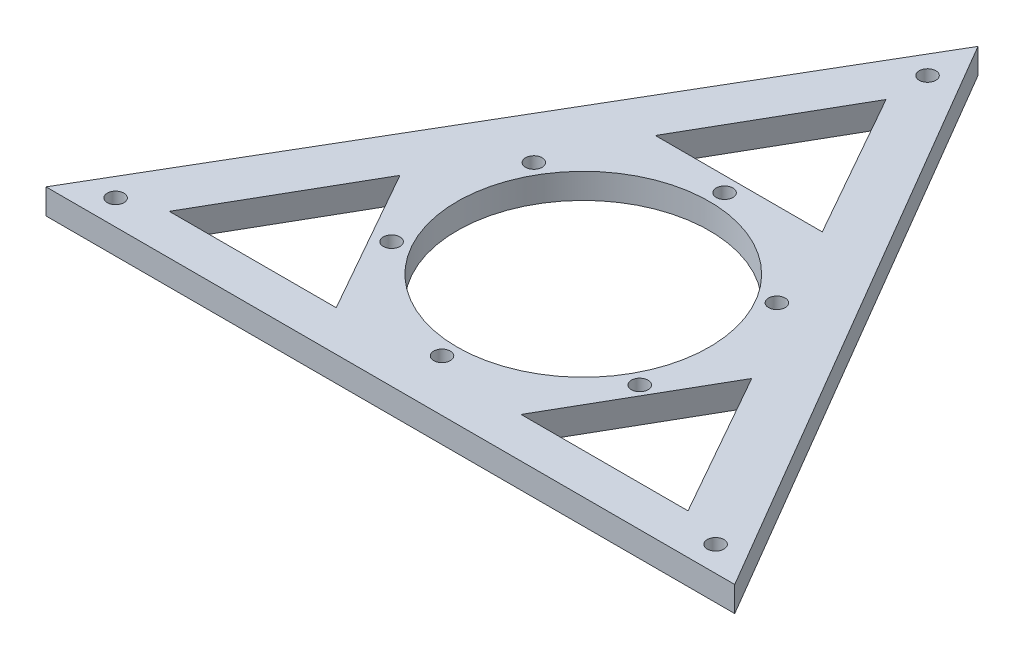
SolidWorks part; units mm, degrees
ref_plane "前视基准面" through (0, 0, 0) normal (0, 0, 1) x (1, 0, 0)
ref_plane "上视基准面" through (0, 0, 0) normal (0, 1, 0) x (1, 0, 0)
ref_plane "右视基准面" through (0, 0, 0) normal (1, 0, 0) x (0, 0, -1)
sketch "草图1" plane through (0, 0, 0) normal (0, 1, 0) x (1, 0, 0)
  line L0 (0, 78.2297) -> (-68.2485, -38.2363)
  line L1 (-68.2485, -38.2363) -> (68.2485, -38.2363)
  line L2 (68.2485, -38.2363) -> (0, 78.2297)
  line L3 (0, 78.2297) -> (0, 60)
  line L4 (-35.1504, -1.1846) -> (-18.7412, -30.2246)
  line L5 (-68.2485, -38.2363) -> (-51.8338, -30.2246)
  line L6 (-51.8338, -30.2246) -> (50.9821, -30.2246)
  line L7 (34.5729, -1.1846) -> (17.8895, -30.2246)
  line L8 (0, 60) -> (-51.8338, -30.2246)
  line L9 (0, 60) -> (50.9821, -30.2246)
  line L11 (-16.6834, 30.96) -> (16.4093, 30.96)
  circle A0 centre (0, 0) radius 78.2297
  circle A1 centre (0, 0) radius 25
extrude "凸台-拉伸1" add sketch "草图1" along normal blind 5 contours L1 L2 L0 A1 | L8 L3 L0 L5 | L11 L8 L4 L6 L7 L9 A1
sketch "草图3" plane through (0, 5, 0) normal (0, 1, 0) x (1, 0, 0)
  line L0 (0, 78.2297) -> (0, -38.2363)
  line L1 (34.1243, 19.9967) -> (-68.2485, -38.2363)
  line L2 (68.2485, -38.2363) -> (-34.1243, 19.9967)
  line L3 (68.2485, -38.2363) -> (0, 78.2297) construction
  line L4 (0, 78.2297) -> (-68.2485, -38.2363) construction
  line L5 (-68.2485, -38.2363) -> (68.2485, -38.2363) construction
  circle A0 centre (0, 0) radius 28
hole_wizard "M4 螺纹孔2" positions "草图12" profile "草图13" tap size "M4" standard "GB"
sketch "草图12" plane through (0, 5, 0) normal (0, 1, 0) x (1, 0, 0)
  line L0 (68.2485, -38.2363) -> (-34.1243, 19.9967) construction
  line L1 (0, 78.2297) -> (0, -38.2363) construction
  line L2 (34.1243, 19.9967) -> (-68.2485, -38.2363) construction
  circle A0 centre (0, 0) radius 28 construction
  point P0 (-24.0823, 14.2844)
  point P6 (0, 28)
  point P10 (24.0823, 14.2844)
  point P14 (24.5857, -13.3995)
  point P16 (0, -28)
  point P18 (-24.5857, -13.3995)
sketch "草图13" plane through (-24.0823, 5, -14.2844) normal (1, 0, 0) x (0, 0, 1)
  line L0 (0, 0) -> (0, 11.0914)
  line L1 (0, 11.0914) -> (1.65, 10.1)
  line L2 (1.65, 10.1) -> (1.65, 0)
  line L5 (1.65, 0) -> (0, 0)
  line L10 (0, 11.0914) -> (-1.65, 10.1) construction
  line L11 (0, -6.35) -> (0, 107.95) construction
  dimension "螺纹孔钻头直径" = 3.3
  dimension "螺纹孔钻头深度" = 10.1
  dimension "导头角度" = 118
cosmetic thread "孔螺蚊线4" parameters "D1"=8, "D2"=4
cosmetic thread "孔螺蚊线5" parameters "D1"=8, "D2"=4
cosmetic thread "孔螺蚊线6" parameters "D1"=8, "D2"=4
cosmetic thread "孔螺蚊线7" parameters "D1"=8, "D2"=4
cosmetic thread "孔螺蚊线8" parameters "D1"=8, "D2"=4
cosmetic thread "孔螺蚊线9" parameters "D1"=8, "D2"=4
hole_wizard "M4 螺纹孔4" positions "草图14" profile "草图15" tap size "M4" standard "GB"
sketch "草图14" plane through (0, 5, 0) normal (0, 1, 0) x (1, 0, 0)
  line L0 (0, 78.2297) -> (0, 68.2297)
  line L1 (0, 78.2297) -> (0, -38.2363) construction
  line L2 (0, 68.2297) -> (-59.4586, -33.2363) construction
  line L3 (34.1243, 19.9967) -> (-68.2485, -38.2363) construction
  line L4 (-59.4586, -33.2363) -> (59.4586, -33.2363) construction
  line L5 (68.2485, -38.2363) -> (-34.1243, 19.9967) construction
  line L6 (59.4586, -33.2363) -> (0, 68.2297) construction
  point P2 (0, 68.2297)
  point P7 (-59.4586, -33.2363)
  point P11 (59.4586, -33.2363)
sketch "草图15" plane through (59.4586, 5, 33.2363) normal (1, 0, 0) x (0, 0, 1)
  line L0 (0, 0) -> (0, 11.0914)
  line L1 (0, 11.0914) -> (1.65, 10.1)
  line L2 (1.65, 10.1) -> (1.65, 0)
  line L5 (1.65, 0) -> (0, 0)
  line L10 (0, 11.0914) -> (-1.65, 10.1) construction
  line L11 (0, -6.35) -> (0, 107.95) construction
  dimension "螺纹孔钻头直径" = 3.3
  dimension "螺纹孔钻头深度" = 10.1
  dimension "导头角度" = 118
cosmetic thread "孔螺蚊线10" parameters "D1"=8, "D2"=4
cosmetic thread "孔螺蚊线11" parameters "D1"=8, "D2"=4
cosmetic thread "孔螺蚊线12" parameters "D1"=8, "D2"=4
sketch "草图16" plane through (0, 5, 0) normal (0, 1, 0) x (1, 0, 0)
  line L0 (0, 78.2297) -> (0, 68.2297)
  line L1 (0, 78.2297) -> (0, -38.2363) construction
